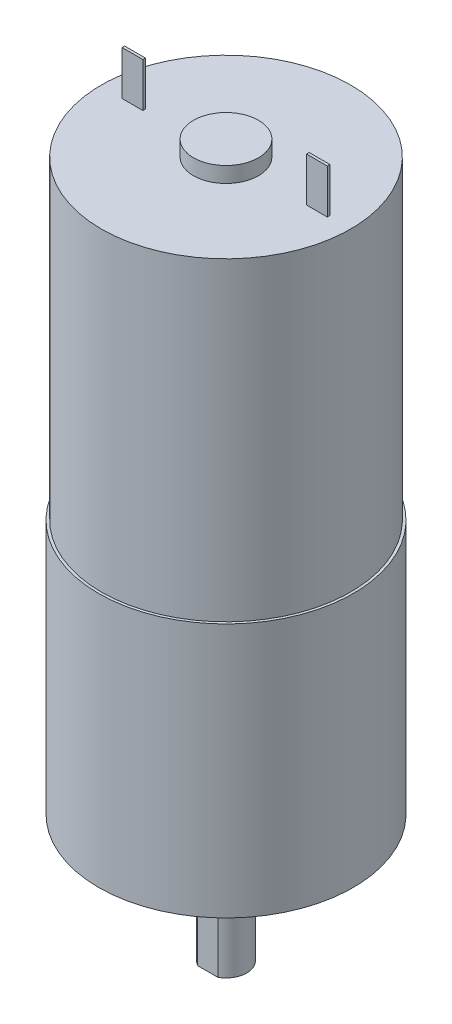
SolidWorks part; units mm, degrees
ref_plane "Front Plane" through (0, 0, 0) normal (0, 0, 1) x (1, 0, 0)
ref_plane "Top Plane" through (0, 0, 0) normal (0, 1, 0) x (1, 0, 0)
ref_plane "Right Plane" through (0, 0, 0) normal (1, 0, 0) x (0, 0, -1)
sketch "Sketch1" plane through (0, 0, 0) normal (0, 1, 0) x (1, 0, 0)
  line L0 (0, 12.446) -> (0, -12.446) construction
  line L1 (-12.446, 0) -> (12.446, 0) construction
  line L2 (-12.446, 0) -> (-9.017, 0) construction
  line L3 (9.017, 0) -> (12.446, 0) construction
  circle A0 centre (0, 0) radius 12.446
  circle A1 centre (-9.017, 0) radius 1.27
  circle A2 centre (9.017, 0) radius 1.27
  dimension "D1" = 24.892
  dimension "D3" = 2.54
  dimension "D4" = 2.54
  dimension "D2" = 18.034
extrude "Boss-Extrude1" add sketch "Sketch1" along normal blind 24.892
sketch "Sketch2" plane through (0, 24.892, 0) normal (0, 1, 0) x (1, 0, 0)
  line L0 (0, 12.446) -> (0, -12.446) construction
  line L1 (-12.446, 0) -> (12.446, 0) construction
  circle A0 centre (0, 0) radius 12.446 construction
hole_wizard "CSK for M3 Flat Head Machine Screw1" positions "Sketch3" profile "Sketch4" countersink size "M3" standard "ANSI Metric" end condition through all
sketch "Sketch3" plane through (0, 24.892, 0) normal (0, 1, 0) x (1, 0, 0)
  line L0 (0, 12.446) -> (0, -12.446) construction
  point P1 (0, 8.1199)
  point P5 (0, -7.587)
sketch "Sketch4" plane through (0, 24.892, -8.1199) normal (1, 0, 0) x (0, 0, 1)
  line L0 (0, 0) -> (0, 24.892)
  line L1 (0, 24.892) -> (1.7, 24.892)
  line L2 (1.7, 24.892) -> (1.7, 1.45)
  line L3 (1.7, 1.45) -> (3.15, 0)
  line L5 (3.15, 0) -> (0, 0)
  line L6 (-1.7, 1.45) -> (-3.15, 0) construction
  line L11 (0, -6.35) -> (0, 107.95) construction
  dimension "Thru Hole Dia." = 3.4
  dimension "Thru Hole Depth" = 24.892
  dimension "Near C'Sink Dia." = 6.3
  dimension "Near C'Sink Angle" = 90
ref_plane "Plane1" through (0, 24.892, 0) normal (0, 1, 0) x (1, 0, 0)
sketch "Sketch5" plane through (0, 24.892, 0) normal (0, 1, 0) x (1, 0, 0)
  circle A0 centre (0, 0) radius 12.192
  dimension "D1" = 24.384
extrude "Boss-Extrude2" add sketch "Sketch5" along normal blind 30.734
sketch "Sketch6" plane through (0, 0, 0) normal (0, 1, 0) x (1, 0, 0)
  circle A0 centre (0, 0) radius 3.556
  dimension "D1" = 7.112
extrude "Boss-Extrude3" add sketch "Sketch6" against normal blind 2.54
ref_plane "Plane2" through (0, -2.54, 0) normal (0, -1, 0) x (-1, 0, 0)
sketch "Sketch7" plane through (0, -2.54, 0) normal (0, -1, 0) x (-1, 0, 0)
  circle A0 centre (0, 0) radius 2.032
  dimension "D1" = 4.064
extrude "Boss-Extrude4" add sketch "Sketch7" along normal blind 9.906
ref_plane "Plane3" through (0, -12.446, 0) normal (0, -1, 0) x (-1, 0, 0)
sketch "Sketch8" plane through (0, -12.446, 0) normal (0, -1, 0) x (-1, 0, 0)
  line L0 (0, 12.446) -> (0, -12.446) construction
  line L1 (-1.016, -1.778) -> (1.016, -1.778)
  line L2 (-1.016, -1.778) -> (-1.016, -2.032)
  line L3 (-1.016, -2.032) -> (1.016, -2.032)
  line L4 (1.016, -1.778) -> (1.016, -2.032)
  line L5 (-1.016, -1.778) -> (1.016, -2.032) construction
  line L6 (-1.016, -2.032) -> (1.016, -1.778) construction
  line L7 (12.446, 0) -> (-12.446, 0) construction
  line L8 (-2.032, 0) -> (2.032, 0) construction
  line L9 (-1.016, 2.032) -> (1.016, 2.032)
  line L10 (1.016, 1.778) -> (1.016, 2.032)
  line L11 (-1.016, 1.778) -> (1.016, 1.778)
  line L12 (-1.016, 1.778) -> (-1.016, 2.032)
  circle A0 centre (0, 0) radius 2.032 construction
  point P0 (0, -1.905)
  dimension "D1" = 0.254
  dimension "D2" = 1.778
  dimension "D3" = 2.032
extrude "Cut-Extrude2" cut sketch "Sketch8" against normal blind 9.906
ref_plane "Plane4" through (0, 55.626, 0) normal (0, 1, 0) x (1, 0, 0)
sketch "Sketch9" plane through (0, 55.626, 0) normal (0, 1, 0) x (1, 0, 0)
  circle A0 centre (0, 0) radius 3.175
  dimension "D1" = 6.35
extrude "Boss-Extrude5" add sketch "Sketch9" along normal blind 1.524
sketch "Sketch10" plane through (0, 55.626, 0) normal (0, 1, 0) x (1, 0, 0)
  line L0 (0, 12.446) -> (0, -12.446) construction
  line L1 (-12.446, 0) -> (12.446, 0) construction
  line L2 (-10.033, -0.127) -> (-8.001, -0.127)
  line L3 (-10.033, -0.127) -> (-10.033, 0.127)
  line L4 (-10.033, 0.127) -> (-8.001, 0.127)
  line L5 (-8.001, -0.127) -> (-8.001, 0.127)
  line L6 (-10.033, -0.127) -> (-8.001, 0.127) construction
  line L7 (-10.033, 0.127) -> (-8.001, -0.127) construction
  line L8 (-12.192, 0) -> (-10.033, 0) construction
  line L9 (10.033, -0.127) -> (8.001, -0.127)
  line L10 (10.033, -0.127) -> (10.033, 0.127)
  line L11 (10.033, 0.127) -> (8.001, 0.127)
  line L12 (8.001, -0.127) -> (8.001, 0.127)
  line L13 (10.033, -0.127) -> (8.001, 0.127) construction
  line L14 (10.033, 0.127) -> (8.001, -0.127) construction
  line L15 (10.033, 0) -> (12.192, 0) construction
  circle A0 centre (0, 0) radius 12.192 construction
  point P4 (-9.017, 0)
  point P11 (9.017, 0)
  dimension "D1" = 18.034
  dimension "D2" = 2.032
  dimension "D3" = 0.254
  dimension "D4" = 2.032
  dimension "D5" = 0.254
extrude "Boss-Extrude6" add sketch "Sketch10" along normal blind 4.318
equation "\"big diameter\" = .98in"
equation "\"screw distance\"= 0.71in"
equation "\"small cross holes\"= 0.10in"
